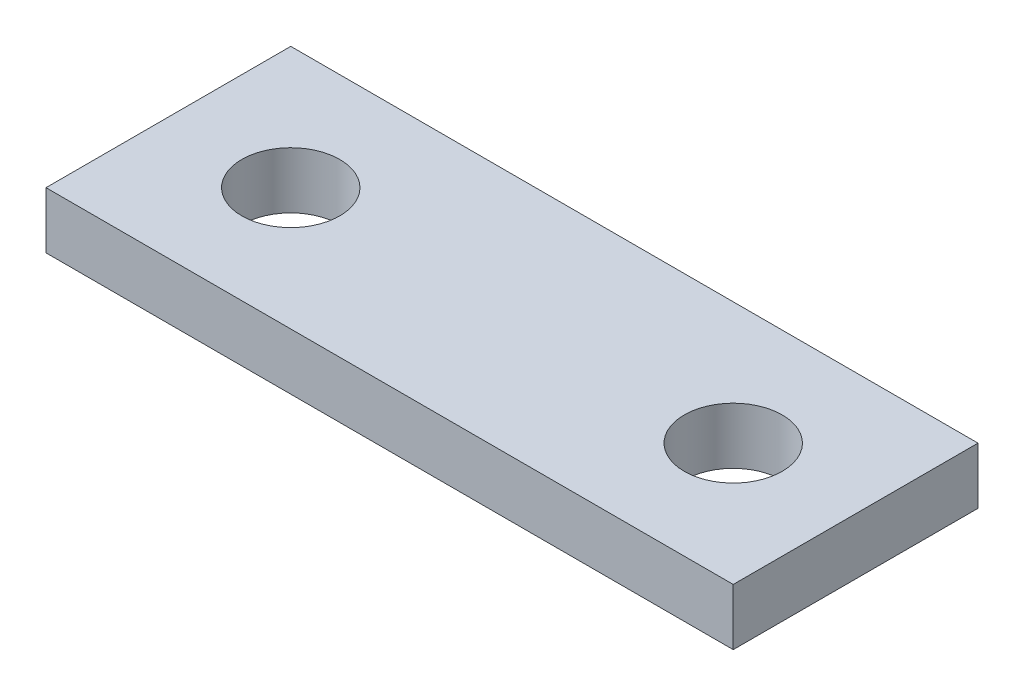
SolidWorks part; units mm, degrees
ref_plane "Plan de face" through (0, 0, 0) normal (0, 0, 1) x (1, 0, 0)
ref_plane "Plan de dessus" through (0, 0, 0) normal (0, 1, 0) x (1, 0, 0)
ref_plane "Plan de droite" through (0, 0, 0) normal (1, 0, 0) x (0, 0, -1)
sketch "Esquisse1" plane through (0, 0, 0) normal (0, 1, 0) x (1, 0, 0)
  line L1 (0, 0) -> (-18.25, 0)
  line L2 (0, 0) -> (0, 13)
  line L3 (0, 13) -> (-18.25, 13)
  line L4 (-18.25, 0) -> (-18.25, 13)
  circle A0 centre (-11.75, 6.5) radius 2.6
  dimension "D5" = 5.2
  dimension "D1" = 13
  dimension "D2" = 18.25
  dimension "D3" = 11.75
  dimension "D4" = 6.5
extrude "Boss.-Extru.1" add sketch "Esquisse1" along normal blind 3
ref_plane "Plan1" through (0, 0, 0) normal (1, 0, 0) x (0, 0, -1)
mirror "Symétrie1" about plane through (0, 0, 0) normal (1, 0, 0) of "Boss.-Extru.1"
